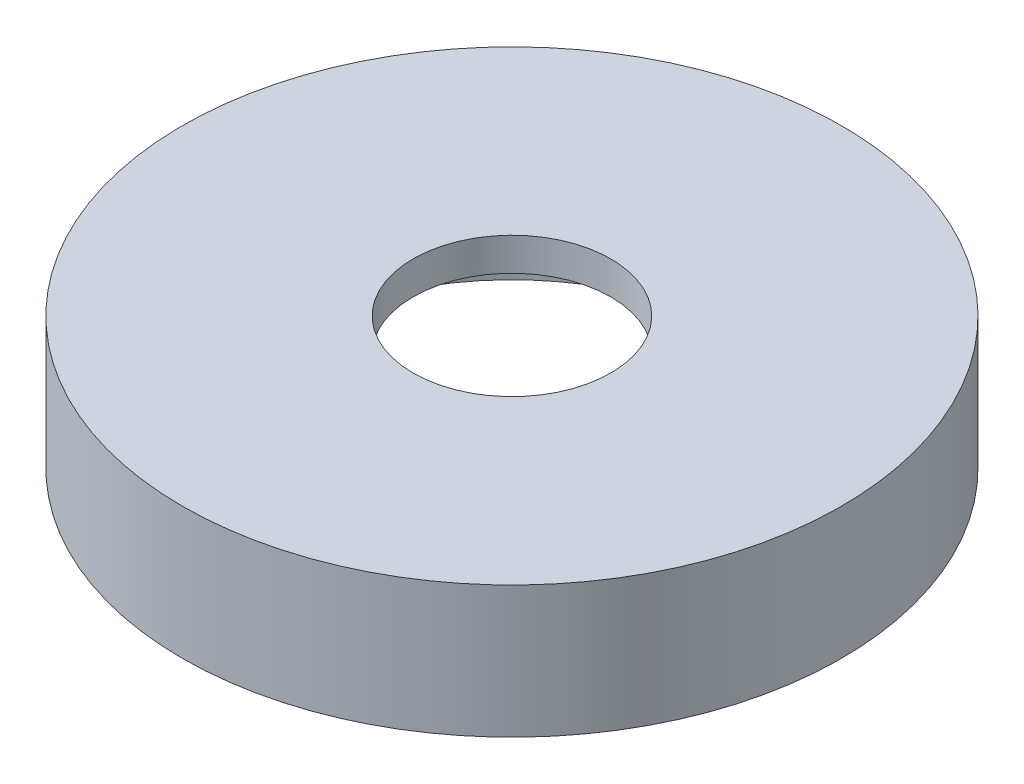
SolidWorks part; units mm, degrees
ref_plane "Front Plane" through (0, 0, 0) normal (0, 0, 1) x (1, 0, 0)
ref_plane "Top Plane" through (0, 0, 0) normal (0, 1, 0) x (1, 0, 0)
ref_plane "Right Plane" through (0, 0, 0) normal (1, 0, 0) x (0, 0, -1)
sketch "Sketch1" plane through (0, 3, 0) normal (0, 1, 0) x (1, 0, 0)
  circle A0 centre (-34.1432, -5.1297) radius 20
extrude "Boss-Extrude1" add sketch "Sketch1" along normal blind 8
sketch "Sketch2" plane through (0, 3, 0) normal (0, -1, 0) x (1, 0, 0)
  circle A0 centre (-34.1432, 5.1297) radius 14
  dimension "D1" = 28
extrude "Cut-Extrude1" cut sketch "Sketch2" against normal blind 6
sketch "Sketch3" plane through (0, 11, 0) normal (0, 1, 0) x (1, 0, 0)
  circle A0 centre (-34.1432, -5.1297) radius 6
  dimension "D1" = 12
extrude "Cut-Extrude4" cut sketch "Sketch3" against normal up to next
hole_wizard "M3x0.5 Tapped Hole1" positions "Sketch5" profile "Sketch4" tap size "M3x0.5" standard "Ansi Metric"
sketch "Sketch5" plane through (0, 3, 0) normal (0, -1, 0) x (1, 0, 0)
  point P0 (-25.6432, 19.8521)
  point P1 (-51.1432, 5.1297)
  point P4 (-25.6432, -9.5927)
sketch "Sketch4" plane through (-25.6432, 3, 19.8521) normal (1, 0, 0) x (0, 0, -1)
  line L0 (0, 0) -> (0, 4.7511)
  line L1 (0, 4.7511) -> (1.25, 4)
  line L2 (1.25, 4) -> (1.25, 0)
  line L5 (1.25, 0) -> (0, 0)
  line L10 (0, 4.7511) -> (-1.25, 4) construction
  line L11 (0, -6.35) -> (0, 107.95) construction
  dimension "Tap Drill Dia." = 2.5
  dimension "Tap Drill Depth" = 4
  dimension "Drill Angle" = 118
cosmetic thread "Hole Thread1" parameters "D1"=4, "D2"=3
cosmetic thread "Hole Thread2" parameters "D1"=4, "D2"=3
cosmetic thread "Hole Thread3" parameters "D1"=4, "D2"=3
sketch "Sketch6" plane through (0, 11, 0) normal (0, 1, 0) x (-1, 0, 0)
  circle A0 centre (34.1432, 5.1297) radius 10 construction
  dimension "D1" = 20
